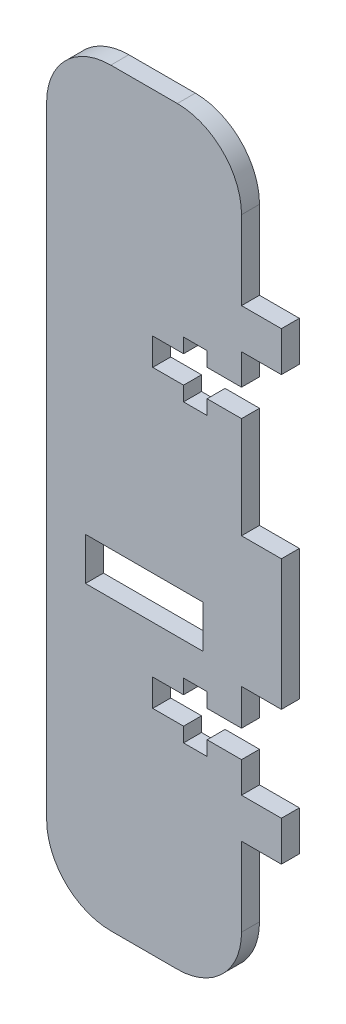
SolidWorks part; units mm, degrees
ref_plane "Front Plane" through (0, 0, 0) normal (0, 0, 1) x (1, 0, 0)
ref_plane "Top Plane" through (0, 0, 0) normal (0, 1, 0) x (1, 0, 0)
ref_plane "Right Plane" through (0, 0, 0) normal (1, 0, 0) x (0, 0, -1)
sketch "Sketch3" plane through (0, 0, 0) normal (0, 0, 1) x (1, 0, 0)
  line L28 (82.0584, -137.9405) -> (97.5656, -137.9405) construction
  line L116 (55.4954, -46.5265) -> (65.8504, -46.5265)
  line L117 (75.8504, -68.7965) -> (75.8504, -56.5265)
  line L118 (75.8504, -68.7965) -> (82.0584, -68.7965)
  line L119 (82.0584, -68.7965) -> (82.0584, -75.0055)
  line L120 (82.0584, -75.0055) -> (75.8504, -75.0055)
  line L121 (75.8504, -75.0055) -> (75.8504, -79.8025)
  line L122 (75.8504, -79.8025) -> (70.4864, -79.8025)
  line L123 (70.4864, -79.8025) -> (70.4864, -77.5455)
  line L124 (70.4864, -77.5455) -> (66.8184, -77.5455)
  line L125 (66.8184, -77.5455) -> (66.8184, -79.8025)
  line L126 (66.8184, -79.8025) -> (62.0204, -79.8025)
  line L127 (62.0204, -79.8025) -> (62.0204, -84.0365)
  line L128 (62.0204, -84.0365) -> (66.8184, -84.0365)
  line L129 (66.8184, -84.0365) -> (66.8184, -86.2935)
  line L130 (66.8184, -86.2935) -> (70.4864, -86.2935)
  line L131 (70.4864, -86.2935) -> (70.4864, -84.0365)
  line L132 (70.4864, -84.0365) -> (75.8504, -84.0365)
  line L133 (75.8504, -84.0365) -> (75.8504, -99.8395)
  line L134 (75.8504, -99.8395) -> (82.0584, -99.8395)
  line L135 (82.0584, -99.8395) -> (82.0584, -120.1605)
  line L136 (82.0584, -120.1605) -> (75.8504, -120.1605)
  line L137 (75.8504, -120.1605) -> (75.8504, -125.8055)
  line L138 (75.8504, -125.8055) -> (70.4864, -125.8055)
  line L139 (70.4864, -125.8055) -> (70.4864, -123.5475)
  line L140 (70.4864, -123.5475) -> (66.8184, -123.5475)
  line L141 (66.8184, -123.5475) -> (66.8184, -125.8055)
  line L142 (66.8184, -125.8055) -> (62.0204, -125.8055)
  line L143 (62.0204, -125.8055) -> (62.0204, -130.0385)
  line L144 (62.0204, -130.0385) -> (66.8184, -130.0385)
  line L145 (66.8184, -130.0385) -> (66.8184, -132.2955)
  line L146 (66.8184, -132.2955) -> (70.4864, -132.2955)
  line L147 (70.4864, -132.2955) -> (70.4864, -130.0385)
  line L148 (70.4864, -130.0385) -> (75.8504, -130.0385)
  line L149 (75.8504, -130.0385) -> (75.8504, -134.8365)
  line L150 (75.8504, -134.8365) -> (82.0584, -134.8365)
  line L151 (82.0584, -134.8365) -> (82.0584, -141.0445)
  line L152 (82.0584, -141.0445) -> (75.8504, -141.0445)
  line L153 (75.8504, -141.0445) -> (75.8504, -153.3157)
  line L154 (55.4954, -163.3157) -> (65.8504, -163.3157)
  line L156 (45.4954, -149.6547) -> (45.4954, -153.3157)
  line L157 (45.4954, -149.6547) -> (45.4954, -56.5265)
  line L158 (51.5398, -118.428) -> (69.8838, -118.428)
  line L159 (51.5398, -118.428) -> (51.5398, -111.7965)
  line L160 (69.8838, -118.428) -> (69.8838, -111.7965)
  line L161 (51.5398, -111.7965) -> (69.8838, -111.7965)
  line L162 (60.7118, 107.4105) -> (60.7118, 0) construction
  line L163 (60.7118, 0) -> (0, 0) construction
  line L164 (60.7118, -111.7965) -> (60.7118, -201.5509) construction
  line L165 (60.7118, -201.5509) -> (60.7118, 0) construction
  line L166 (82.0584, -110) -> (60.7118, -110) construction
  arc A20 (75.8504, -153.3157) -> (65.8504, -163.3157) centre (65.8504, -153.3157) cw
  arc A21 (55.4954, -163.3157) -> (45.4954, -153.3157) centre (55.4954, -153.3157) cw
  arc A22 (75.8504, -56.5265) -> (65.8504, -46.5265) centre (65.8504, -56.5265) ccw
  arc A23 (45.4954, -56.5265) -> (55.4954, -46.5265) centre (55.4954, -56.5265) cw
  point P5 (0, 0)
  dimension "D1" = 10
  dimension "D2" = 27.9405
  dimension "D3" = 18.344
  dimension "D4" = 36.563
  dimension "D5" = 110
  dimension "D6" = 20.321
  dimension "D7" = 60.7118
  dimension "D8" = 46.5265
  dimension "D9" = 6.6315
  dimension "D10" = 14.676
  dimension "D11" = 6.208
  dimension "D12" = 6.208
  dimension "D13" = 116.7892
  dimension "D14" = 6.208
  dimension "D15" = 22.27
  dimension "D16" = 43
extrude "Boss-Extrude2" add sketch "Sketch3" along normal blind 2.8
